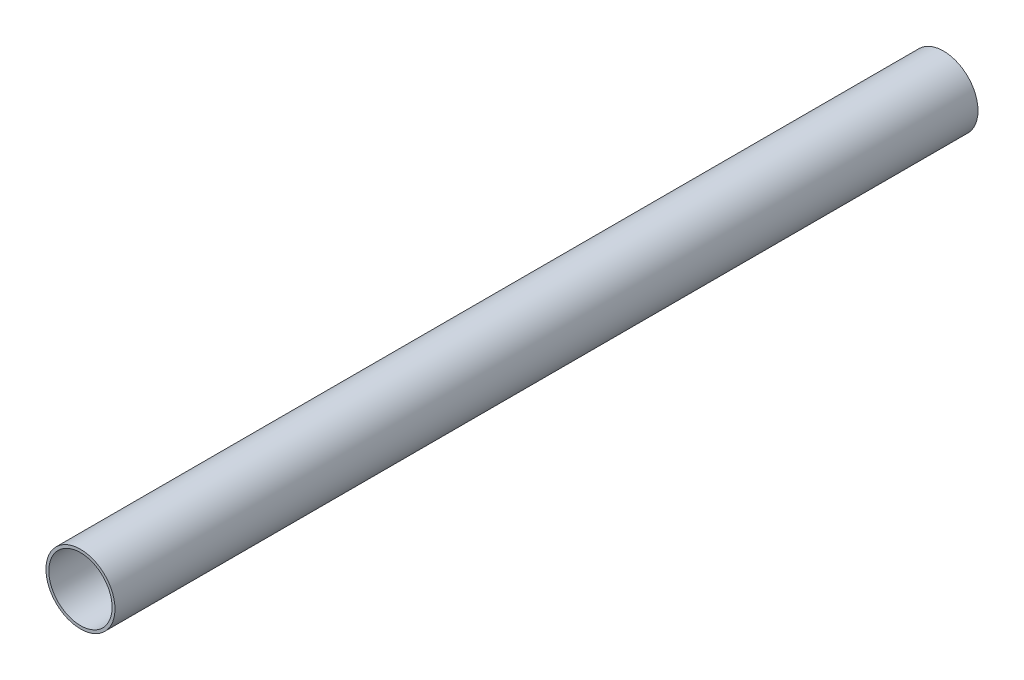
SolidWorks part; units mm, degrees
ref_plane "Plan de face" through (0, 0, 0) normal (0, 0, 1) x (1, 0, 0)
ref_plane "Plan de dessus" through (0, 0, 0) normal (0, 1, 0) x (1, 0, 0)
ref_plane "Plan de droite" through (0, 0, 0) normal (1, 0, 0) x (0, 0, -1)
sketch "Esquisse1" plane through (0, 0, 0) normal (0, 0, 1) x (1, 0, 0)
  circle A0 centre (0, 0) radius 12
  circle A1 centre (0, 0) radius 11
  dimension "D1" = 24
  dimension "D2" = 22
extrude "Boss.-Extru.1" add sketch "Esquisse1" along normal blind 300
